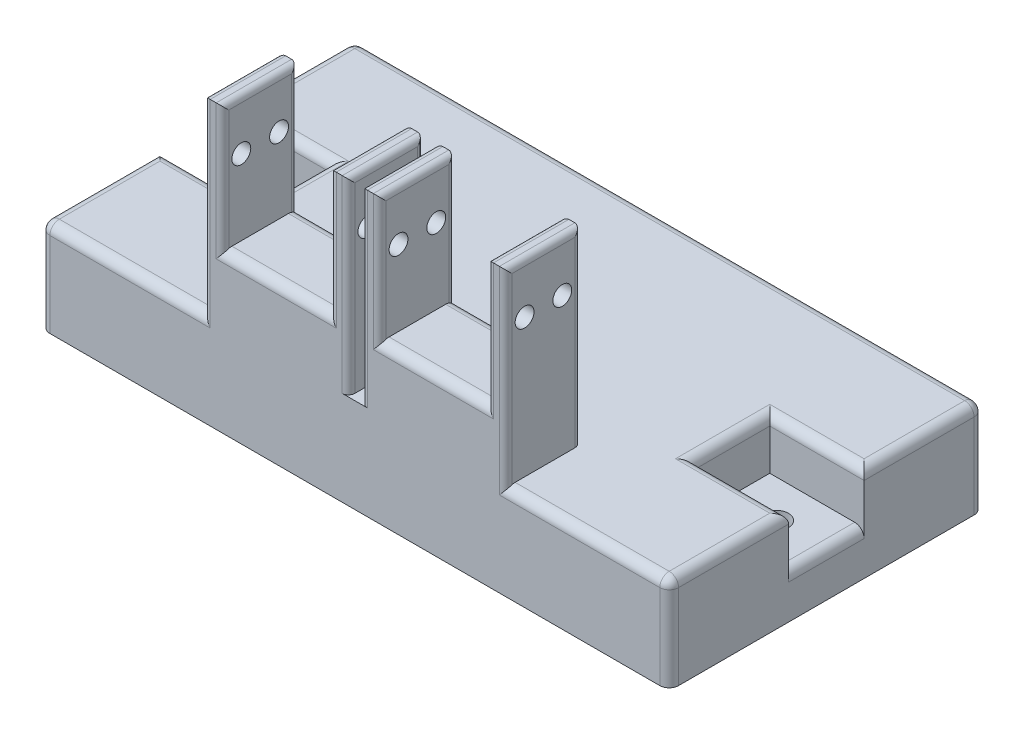
SolidWorks part; units mm, degrees
ref_plane "Front Plane" through (0, 0, 0) normal (0, 0, 1) x (1, 0, 0)
ref_plane "Top Plane" through (0, 0, 0) normal (0, 1, 0) x (1, 0, 0)
ref_plane "Right Plane" through (0, 0, 0) normal (1, 0, 0) x (0, 0, -1)
sketch "Sketch1" plane through (0, 0, 0) normal (0, 1, 0) x (1, 0, 0)
  line L1 (-50, 25) -> (50, 25)
  line L2 (-50, 25) -> (-50, -25)
  line L3 (-50, -25) -> (50, -25)
  line L4 (50, 25) -> (50, -25)
  line L5 (-50, 25) -> (50, -25) construction
  line L6 (-50, -25) -> (50, 25) construction
  point P0 (0, 0)
  dimension "D1" = 50
  dimension "D2" = 100
extrude "Boss-Extrude1" add sketch "Sketch1" along normal blind 15
sketch "Sketch2" plane through (0, 15, 0) normal (0, 1, 0) x (1, 0, 0)
  line L0 (-50, 25) -> (-50, -25) construction
  line L1 (-65, -6) -> (-35, -6)
  line L2 (-65, -6) -> (-65, 6)
  line L3 (-65, 6) -> (-35, 6)
  line L4 (-35, -6) -> (-35, 6)
  line L5 (-65, -6) -> (-35, 6) construction
  line L6 (-65, 6) -> (-35, -6) construction
  line L7 (0, 0) -> (0, 33.6115) construction
  line L8 (65, 6) -> (35, 6)
  line L9 (35, -6) -> (35, 6)
  line L10 (65, -6) -> (35, -6)
  line L11 (65, -6) -> (65, 6)
  point P0 (-50, 0)
  dimension "D1" = 12
  dimension "D2" = 15
extrude "Cut-Extrude1" cut sketch "Sketch2" against normal blind 8
sketch "Sketch5" plane through (0, 15, 0) normal (0, 1, 0) x (1, 0, 0)
  line L0 (-39.0612, 0) -> (46.6537, 0) construction
  line L1 (0, 18.1819) -> (0, -19.7804) construction
  line L2 (25, 18.1819) -> (25, -18.1819) construction
  line L3 (12.5, 17.2133) -> (12.5, -14.4718) construction
  dimension "D1" = 25
  dimension "D2" = 12.5
sketch "Sketch7" plane through (0, 15, 0) normal (0, 1, 0) x (1, 0, 0)
  line L1 (1, -13) -> (24, -13)
  line L2 (1, -13) -> (1, -25)
  line L3 (1, -25) -> (24, -25)
  line L4 (24, -13) -> (24, -25)
  line L5 (1, -13) -> (24, -25) construction
  line L6 (1, -25) -> (24, -13) construction
  line L9 (-50, -25) -> (50, -25) construction
  point P0 (12.5, 0)
  dimension "D1" = 23
  dimension "D2" = 12
extrude "Boss-Extrude2" add sketch "Sketch7" along normal blind 10
sketch "Sketch8" plane through (0, 25, 0) normal (0, 1, 0) x (1, 0, 0)
  line L0 (1, -13) -> (1, -25)
  line L1 (1, -13) -> (3.95, -13)
  line L2 (1, -25) -> (3.95, -25)
  line L3 (3.95, -13) -> (3.95, -25)
  line L4 (1, -13) -> (1, -25) construction
  line L8 (24, -13) -> (24, -25)
  line L9 (24, -13) -> (21.05, -13)
  line L10 (24, -25) -> (21.05, -25)
  line L11 (21.05, -13) -> (21.05, -25)
  dimension "D1" = 2.95
  dimension "D2" = 2.95
extrude "Boss-Extrude3" add sketch "Sketch8" along normal blind 20
sketch "Sketch10" plane through (1, 0, 0) normal (-1, 0, 0) x (0, 0, 1)
  line L1 (19, 45) -> (19, 29.4352) construction
  line L2 (13, 45) -> (25, 45) construction
  line L6 (25, 45) -> (25, 15) construction
  circle A2 centre (16, 37) radius 1.5
  circle A4 centre (22, 37) radius 1.5
  dimension "D1" = 3
  dimension "D2" = 8
extrude "Cut-Extrude2" cut sketch "Sketch10" against normal through all
mirror "Mirror1" about plane through (0, 0, 0) normal (1, 0, 0) of "Boss-Extrude3", "Cut-Extrude2", "Boss-Extrude2"
fillet "Fillet1" radius 1.5 23 edges at (37, 15, 25) (-37, 15, 25) (-50, 15, 15.5) (-50, 15, -15.5) (0, 15, -25) (50, 15, -15.5) (50, 15, 15.5) (-50, 7, 0) (50, 7, 0) (42.5, 15, 6) (35, 15, 0) (42.5, 15, -6) (-35, 15, 0) (-42.5, 15, -6) (-42.5, 15, 6) (12.5, 25, 13) (12.5, 25, 25) (-12.5, 25, 25) (-12.5, 25, 13) (50, 7.5, 25) (50, 7.5, -25) (-50, 7.5, -25) (-50, 7.5, 25)
fillet "Fillet2" radius 1 24 edges at (24, 45, 19) (21.05, 45, 19) (3.95, 45, 19) (1, 45, 19) (-1, 45, 19) (-3.95, 45, 19) (-24, 45, 19) (-21.05, 45, 19) (-21.05, 34.25, 13) (-3.95, 34.25, 13) (-1, 30, 13) (-1, 30, 25) (1, 30, 13) (3.95, 34.25, 13) (21.05, 34.25, 13) (24, 30, 13) (-24, 30, 13) (24, 29.25, 25) (21.05, 34.25, 25) (3.95, 34.25, 25) (1, 30, 25) (-3.95, 34.25, 25) (-24, 29.25, 25) (-21.05, 34.25, 25)
sketch "Sketch11" plane through (0, 7, 0) normal (0, 1, 0) x (1, 0, 0)
  line L0 (-39.0612, 0) -> (46.6537, 0) construction
  line L1 (35, 6) -> (35, -6) construction
  circle A0 centre (42, 0) radius 1.975
  dimension "D1" = 7
  dimension "D2" = 3.95
extrude "Cut-Extrude3" cut sketch "Sketch11" against normal blind 20
sketch "Sketch12" plane through (0, 7, 0) normal (0, 1, 0) x (1, 0, 0)
  line L0 (-35, -6) -> (-35, 6) construction
  circle A0 centre (-42, 0) radius 1.975
  dimension "D1" = 7
  dimension "D2" = 3.95
extrude "Cut-Extrude4" cut sketch "Sketch12" against normal blind 20
